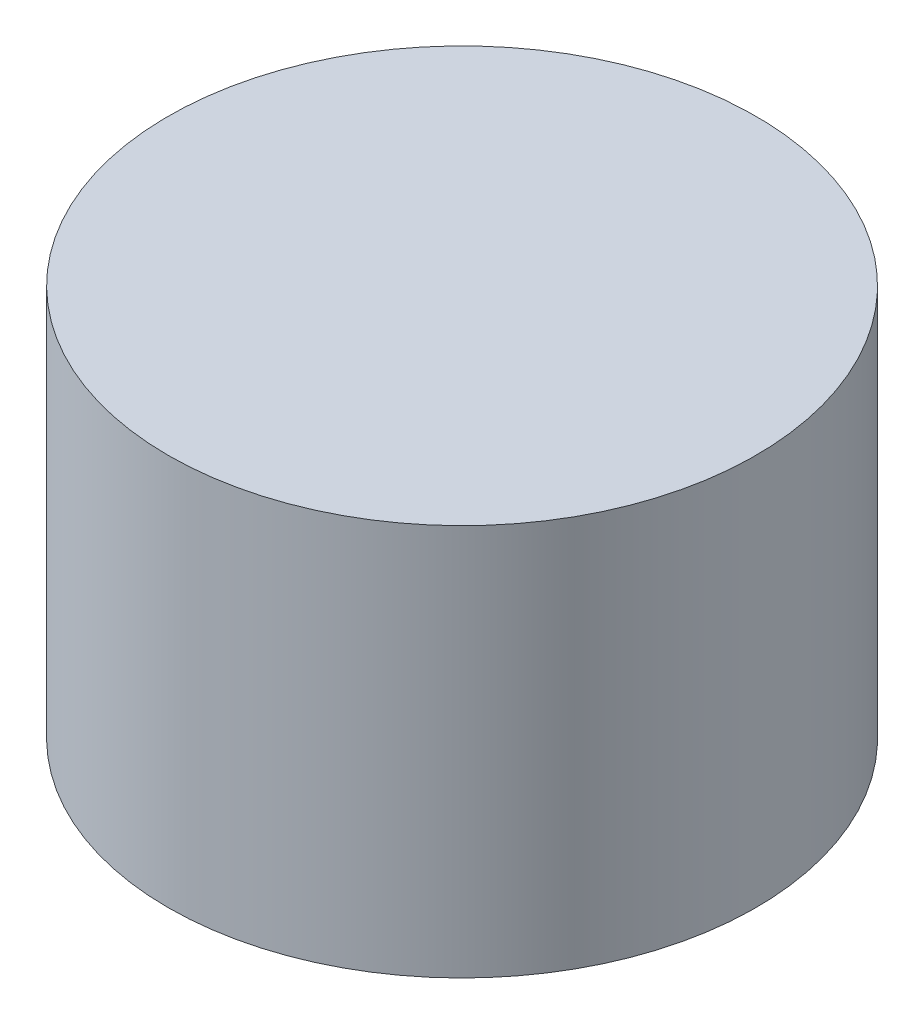
SolidWorks part; units mm, degrees
material "1060 Alloy"
ref_plane "Front Plane" through (0, 0, 0) normal (0, 0, 1) x (1, 0, 0)
ref_plane "Top Plane" through (0, 0, 0) normal (0, 1, 0) x (1, 0, 0)
ref_plane "Right Plane" through (0, 0, 0) normal (1, 0, 0) x (0, 0, -1)
sketch "Sketch1" plane through (0, 0, 0) normal (0, 1, 0) x (1, 0, 0)
  circle A0 centre (0, 0) radius 15
  dimension "D1" = 30
extrude "Boss-Extrude1" add sketch "Sketch1" along normal blind 20
